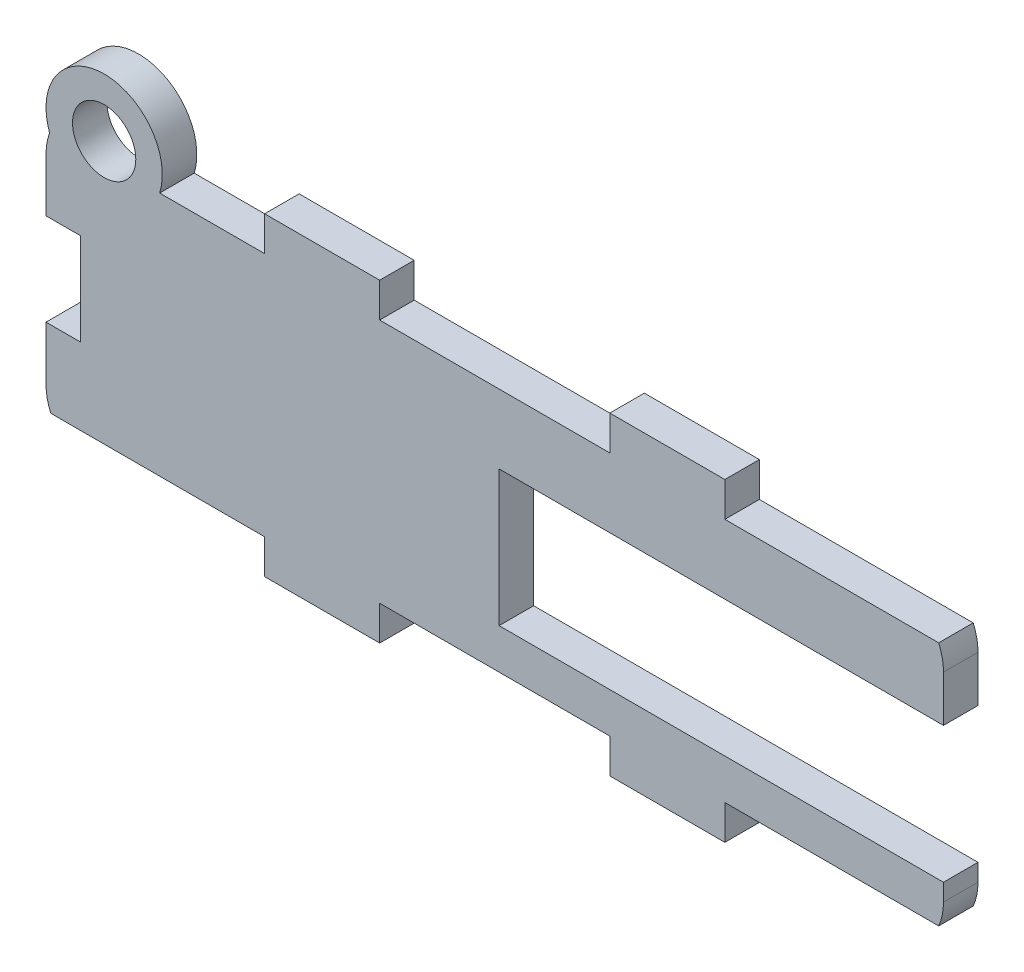
SolidWorks part; units mm, degrees
ref_plane "Front Plane" through (0, 0, 0) normal (0, 0, 1) x (1, 0, 0)
ref_plane "Top Plane" through (0, 0, 0) normal (0, 1, 0) x (1, 0, 0)
ref_plane "Right Plane" through (0, 0, 0) normal (1, 0, 0) x (0, 0, -1)
sketch "Sketch1" plane through (0, 0, 0) normal (0, 0, 1) x (1, 0, 0)
  line L0 (52, -3) -> (52, 0) construction
  line L1 (-7, -3) -> (3, -3)
  line L2 (-26, 2) -> (-26, 19.3118)
  line L3 (-7, 24.3118) -> (3, 24.3118)
  line L4 (52, 2) -> (52, 19.3118)
  line L5 (-26, -3) -> (52, 24.3118) construction
  line L6 (-26, 24.3118) -> (52, -3) construction
  line L7 (23, -3) -> (33, -3)
  line L8 (-7, 0) -> (-25.5826, 0)
  line L9 (-7, 0) -> (-7, -3)
  line L12 (-7, 0) -> (-26, -3) construction
  line L13 (-7, -3) -> (-26, 0) construction
  line L15 (3, -3) -> (3, 0)
  line L16 (3, 0) -> (23, 0)
  line L17 (23, -3) -> (23, 0)
  line L18 (3, -3) -> (23, 0) construction
  line L19 (3, 0) -> (23, -3) construction
  line L21 (33, -3) -> (33, 0)
  line L22 (33, 0) -> (51.5826, 0)
  line L24 (33, -3) -> (52, 0) construction
  line L25 (33, 0) -> (52, -3) construction
  line L27 (-33.6771, 10.6559) -> (59.6771, 10.6559) construction
  line L28 (33, 24.3118) -> (33, 21.3118)
  line L29 (23, 24.3118) -> (33, 24.3118)
  line L30 (23, 24.3118) -> (23, 21.3118)
  line L31 (3, 24.3118) -> (3, 21.3118)
  line L32 (-7, 21.3118) -> (-7, 24.3118)
  line L33 (3, 0) -> (-7, 0) construction
  line L34 (-7, 21.3118) -> (-25.5826, 21.3118)
  line L35 (3, 21.3118) -> (23, 21.3118)
  line L36 (33, 21.3118) -> (51.5826, 21.3118)
  line L37 (-7, 0) -> (-10, 0) construction
  arc A1 (-26, 19.3118) -> (-25.5826, 21.3118) centre (-21, 19.3118) cw
  arc A2 (51.5826, 21.3118) -> (52, 19.3118) centre (47, 19.3118) cw
  arc A4 (-25.5826, 0) -> (-26, 2) centre (-21, 2) cw
  arc A5 (51.5826, 0) -> (52, 2) centre (47, 2) ccw
  point P4 (13, 10.6559)
  point P24 (-16.5, -1.5)
  point P29 (13, -1.5)
  point P35 (42.5, -1.5)
  point P41 (13, 10.6559)
  point P49 (0, 0)
  point P50 (33, -3)
  point P52 (0, 0)
  point P53 (-7, 0)
extrude "Boss-Extrude1" add sketch "Sketch1" along normal blind 3
sketch "Sketch2" plane through (0, 0, 3) normal (0, 0, 1) x (1, 0, 0)
  line L0 (13.38, 3.5) -> (13.38, 15.3) construction
  line L1 (13.38, 15.3) -> (23.54, 15.3) construction
  line L2 (13.38, 3.5) -> (13.38, 15.3)
  line L3 (13.38, 15.3) -> (23.54, 15.3)
  line L4 (23.54, 15.3) -> (52, 15.3)
  line L5 (52, 2) -> (52, 19.3118) construction
  line L7 (13.38, 3.5) -> (52, 3.5)
  line L8 (52, 3.5) -> (52, 15.3)
extrude "Cut-Extrude1" cut sketch "Sketch2" against normal up to next
sketch "Sketch3" plane through (0, 0, 3) normal (0, 0, 1) x (1, 0, 0)
  line L0 (-7, 22.8118) -> (-23, 22.8118) construction
  line L1 (-7, 24.3118) -> (-7, 21.3118) construction
  line L2 (-23, 24.3118) -> (-23, 21.3118) construction
  line L4 (-7, 21.3118) -> (-25.5826, 21.3118) construction
  circle A4 centre (-20.9461, 22.8118) radius 2.7498
  circle A5 centre (-20.9461, 22.8118) radius 5.0539
extrude "Boss-Extrude2" add sketch "Sketch3" against normal blind 3
sketch "Sketch4" plane through (0, 0, 3) normal (0, 0, 1) x (1, 0, 0)
  line L0 (-23.2507, 21.3118) -> (-18.6415, 21.3118)
  line L2 (-20.9461, 21.3118) -> (-20.9461, 25.5616) construction
  arc A1 (-18.6415, 21.3118) -> (-23.2507, 21.3118) centre (-20.9461, 22.8118) ccw construction
  arc A2 (-23.2507, 21.3118) -> (-18.6415, 21.3118) centre (-20.9461, 22.8118) ccw
extrude "Cut-Extrude2" cut sketch "Sketch4" against normal up to next
sketch "Sketch5" plane through (0, 0, 3) normal (0, 0, 1) x (1, 0, 0)
  line L0 (-26, 19.3118) -> (-26, 2) construction
  line L1 (-23, 6.6559) -> (-26, 6.6559)
  line L2 (-23, 6.6559) -> (-23, 14.6559)
  line L3 (-23, 14.6559) -> (-26, 14.6559)
  line L4 (-26, 6.6559) -> (-26, 14.6559)
  line L5 (-23, 6.6559) -> (-26, 14.6559) construction
  line L6 (-23, 14.6559) -> (-26, 6.6559) construction
  point P4 (-24.5, 10.6559)
  point P8 (-26, 15.1656)
  dimension "D1" = 8
extrude "Cut-Extrude3" cut sketch "Sketch5" against normal blind 3 contours L2 L3 L4 L1
